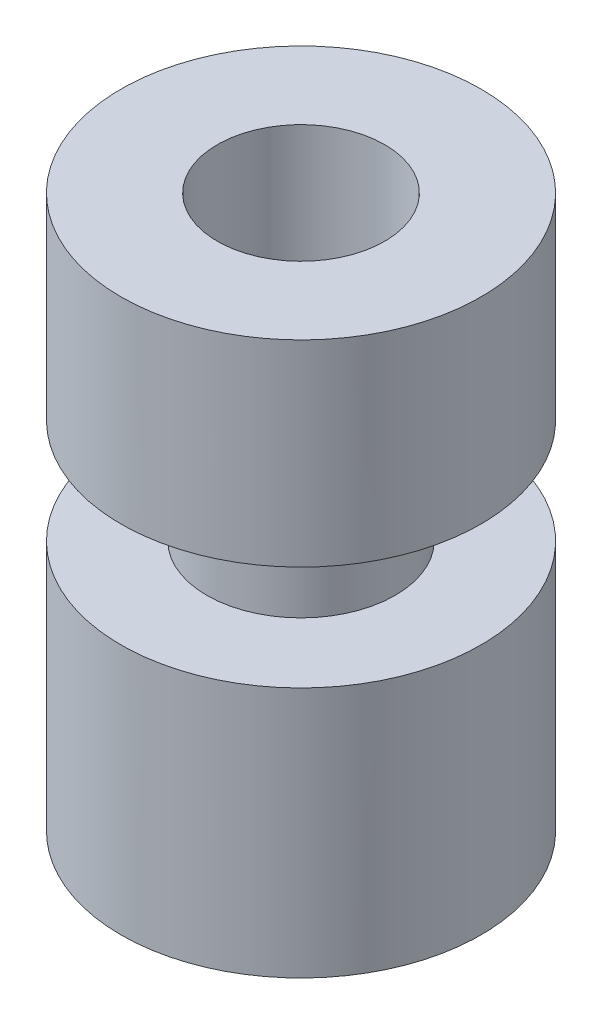
SolidWorks part; units mm, degrees
ref_plane "Front Plane" through (0, 0, 0) normal (0, 0, 1) x (1, 0, 0)
ref_plane "Top Plane" through (0, 0, 0) normal (0, 1, 0) x (1, 0, 0)
ref_plane "Right Plane" through (0, 0, 0) normal (1, 0, 0) x (0, 0, -1)
sketch "Sketch1" plane through (0, 0, 0) normal (0, 1, 0) x (1, 0, 0)
  circle A0 centre (0, 0) radius 2.15
  dimension "D1" = 4.3
extrude "Boss-Extrude1" add sketch "Sketch1" along normal blind 6.6
sketch "Sketch2" plane through (0, 0, 0) normal (0, -1, 0) x (1, 0, 0)
  circle A0 centre (0, 0) radius 1
  dimension "D1" = 2
extrude "Cut-Extrude1" cut sketch "Sketch2" against normal through all
ref_plane "Plane1" through (0, 4.25, 0) normal (0, -1, 0) x (-1, 0, 0)
sketch "Sketch3" plane through (0, 4.25, 0) normal (0, -1, 0) x (-1, 0, 0)
  circle A0 centre (0, 0) radius 2.15 construction
  circle A1 centre (0, 0) radius 2.15
  circle A2 centre (0, 0) radius 1.125
  dimension "D1" = 2.25
extrude "Cut-Extrude2" cut sketch "Sketch3" along normal blind 1.25
